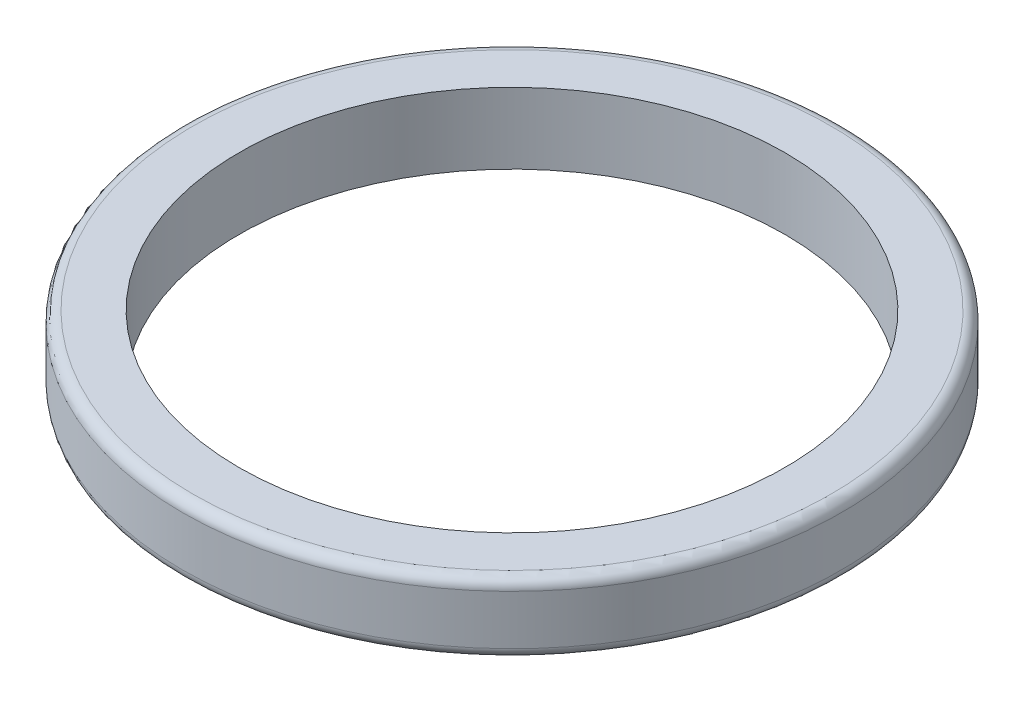
SolidWorks part; units mm, degrees
ref_plane "Front Plane" through (0, 0, 0) normal (0, 0, 1) x (1, 0, 0)
ref_plane "Top Plane" through (0, 0, 0) normal (0, 1, 0) x (1, 0, 0)
ref_plane "Right Plane" through (0, 0, 0) normal (1, 0, 0) x (0, 0, -1)
sketch "Sketch1" plane through (0, 0, 0) normal (0, 1, 0) x (1, 0, 0)
  circle A0 centre (0, 0) radius 12.8333
  circle A1 centre (0, 0) radius 15.5
  dimension "D1" = 25.6667
  dimension "D2" = 2.6667
extrude "Boss-Extrude2" add sketch "Sketch1" along normal blind 3.3333
fillet "Fillet1" radius 0.5 2 edges at (0, 0, 15.5) (0, 3.3333, 15.5)
